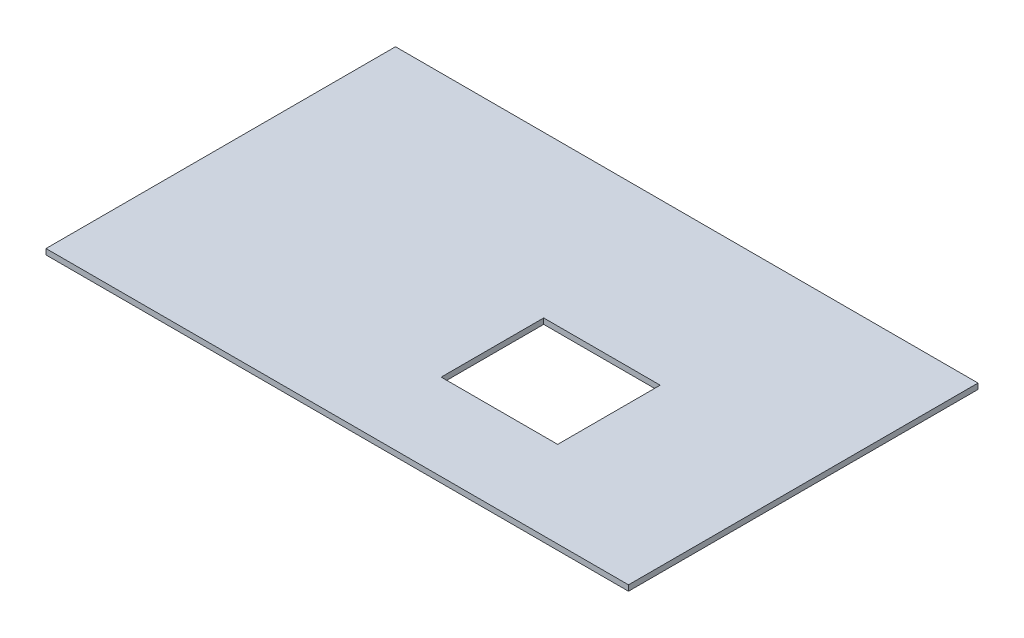
SolidWorks part; units mm, degrees
ref_plane "Front Plane" through (0, 0, 0) normal (0, 0, 1) x (1, 0, 0)
ref_plane "Top Plane" through (0, 0, 0) normal (0, 1, 0) x (1, 0, 0)
ref_plane "Right Plane" through (0, 0, 0) normal (1, 0, 0) x (0, 0, -1)
sketch "Sketch1" plane through (0, 0, 0) normal (0, 1, 0) x (1, 0, 0)
  line L1 (62.5, -37.5) -> (-62.5, -37.5)
  line L2 (62.5, -37.5) -> (62.5, 37.5)
  line L3 (62.5, 37.5) -> (-62.5, 37.5)
  line L4 (-62.5, -37.5) -> (-62.5, 37.5)
  line L5 (62.5, -37.5) -> (-62.5, 37.5) construction
  line L6 (62.5, 37.5) -> (-62.5, -37.5) construction
  line L11 (25.8, -19) -> (3.8, -19)
  line L12 (25.8, -19) -> (25.8, 3)
  line L13 (25.8, 3) -> (3.8, 3)
  line L14 (3.8, -19) -> (3.8, 3)
  line L15 (25.8, -19) -> (3.8, 3) construction
  line L16 (25.8, 3) -> (3.8, -19) construction
  point P0 (0, 0)
  point P6 (14.8, -8)
  dimension "D1" = 125
  dimension "D2" = 75
  dimension "D3" = 47.7
  dimension "D4" = 29.5
  dimension "D5" = 22
extrude "Boss-Extrude1" add sketch "Sketch1" along normal blind 1.2
sketch "Sketch2" plane through (0, 1.2, 0) normal (0, 1, 0) x (1, 0, 0)
  line L0 (3.8, -19) -> (25.8, -19) construction
  line L1 (25.8, 3) -> (28.8, 3)
  line L2 (25.8, 3) -> (25.8, -19)
  line L3 (25.8, -19) -> (28.8, -19)
  line L4 (28.8, 3) -> (28.8, -19)
  dimension "D1" = 3
extrude "Cut-Extrude1" cut sketch "Sketch2" against normal through all both and the other way through all
